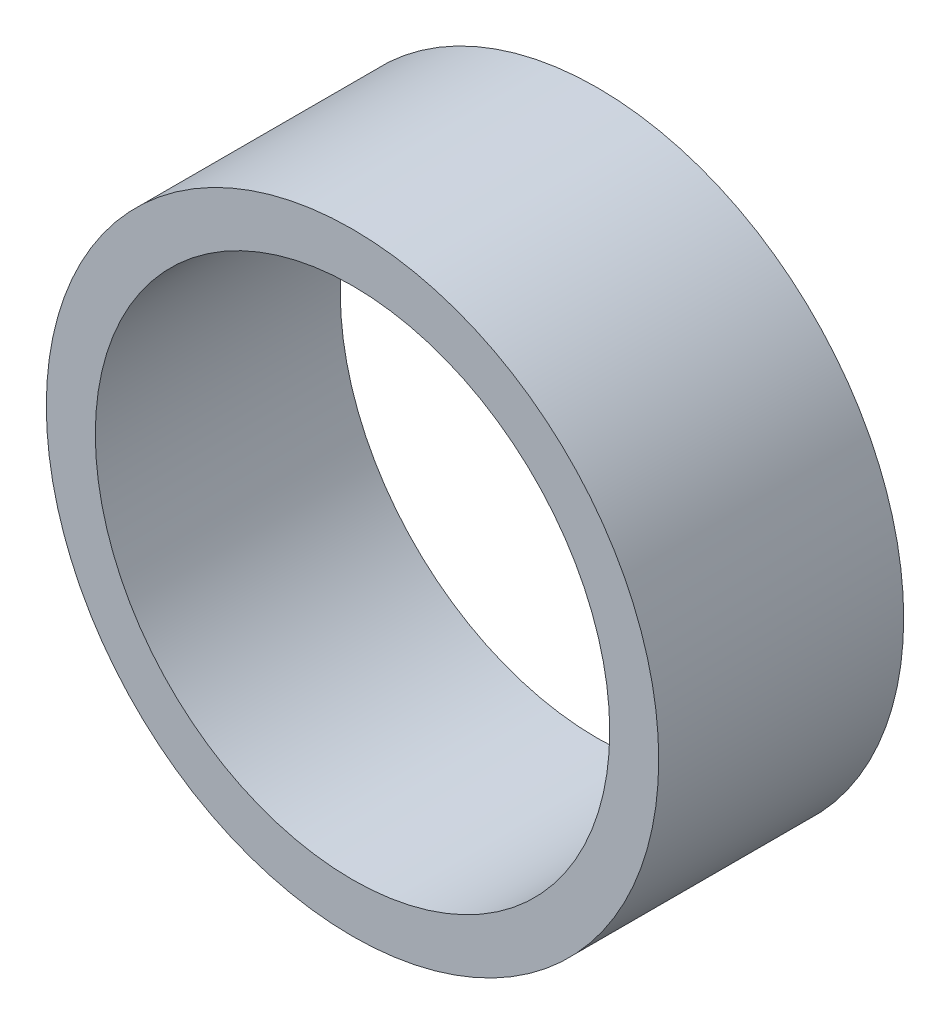
SolidWorks part; units mm, degrees
ref_plane "Front Plane" through (0, 0, 0) normal (0, 0, 1) x (1, 0, 0)
ref_plane "Top Plane" through (0, 0, 0) normal (0, 1, 0) x (1, 0, 0)
ref_plane "Right Plane" through (0, 0, 0) normal (1, 0, 0) x (0, 0, -1)
sketch "Sketch1" plane through (0, 0, 0) normal (0, 0, 1) x (1, 0, 0)
  circle A0 centre (0, 8.25) radius 5
  dimension "D1" = 10
extrude "Boss-Extrude1" add sketch "Sketch1" against normal blind 4
sketch "Sketch3" plane through (0, 0, 0) normal (0, 0, 1) x (1, 0, 0)
  circle A0 centre (0, 8.25) radius 4.2
  dimension "D1" = 8.4
extrude "Cut-Extrude1" cut sketch "Sketch3" against normal through all
